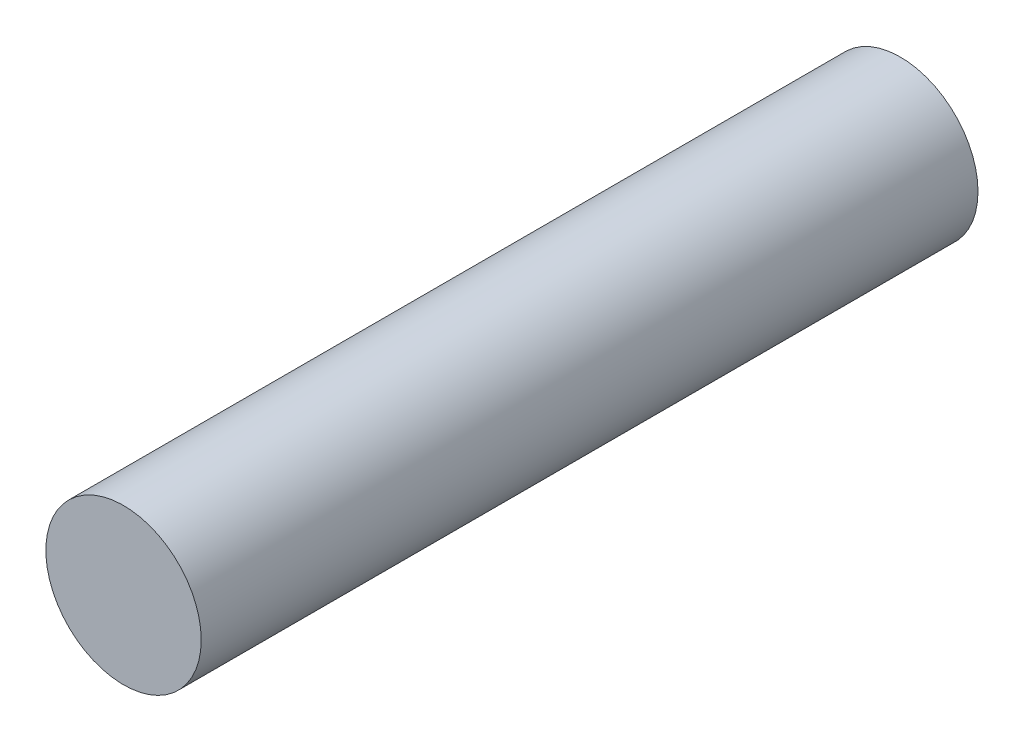
SolidWorks part; units mm, degrees
ref_plane "Front Plane" through (0, 0, 0) normal (0, 0, 1) x (1, 0, 0)
ref_plane "Top Plane" through (0, 0, 0) normal (0, 1, 0) x (1, 0, 0)
ref_plane "Right Plane" through (0, 0, 0) normal (1, 0, 0) x (0, 0, -1)
sketch "Sketch1" plane through (0, 0, 0) normal (0, 0, 1) x (1, 0, 0)
  circle A0 centre (0, 0) radius 2
  dimension "D1" = 4
extrude "Boss-Extrude1" add sketch "Sketch1" along normal blind 20 contours A0
